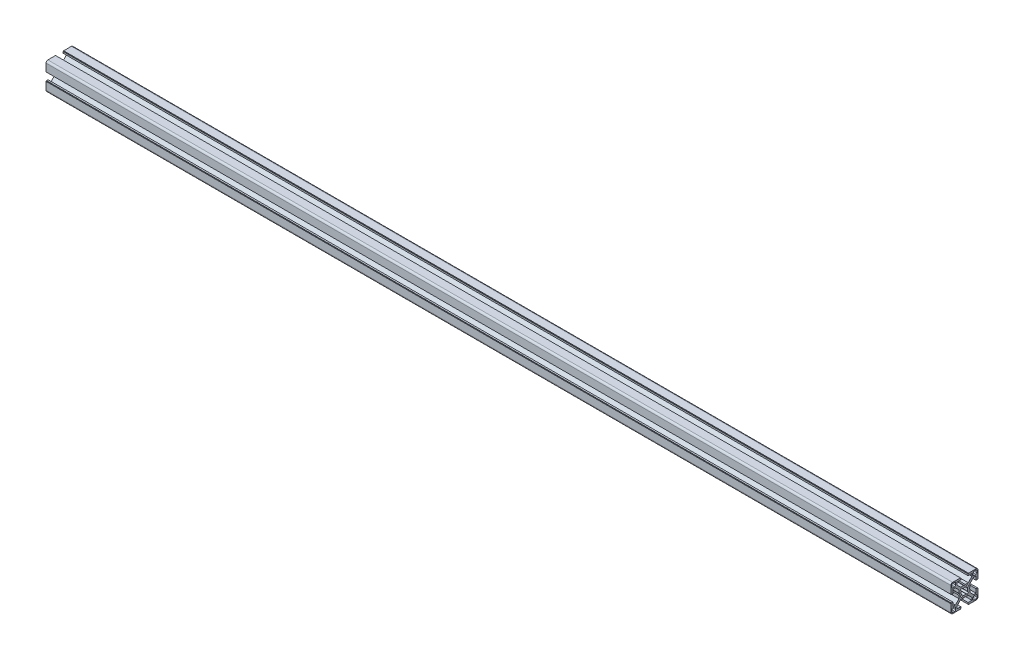
SolidWorks part; units mm, degrees
ref_plane "Piano frontale" through (0, 0, 0) normal (0, 0, 1) x (1, 0, 0)
ref_plane "Piano superiore" through (0, 0, 0) normal (0, 1, 0) x (1, 0, 0)
ref_plane "Piano destro" through (0, 0, 0) normal (1, 0, 0) x (0, 0, -1)
ref_plane "Piano1" through (0, 0, 0) normal (-1, 0, 0) x (0, -1, 0)
sketch "Schizzo1" plane through (0, 0, 0) normal (-1, 0, 0) x (0, -1, 0)
  line L0 (-3.1172, 4.5314) -> (-1.6168, 3.2724)
  line L1 (1.6168, 3.2724) -> (3.1172, 4.5314)
  line L2 (4.5314, 3.1172) -> (3.2724, 1.6168)
  line L3 (3.2724, -1.6168) -> (4.5314, -3.1172)
  line L4 (3.1172, -4.5314) -> (1.6168, -3.2724)
  line L5 (-1.6168, -3.2724) -> (-3.1172, -4.5314)
  line L6 (-4.5314, -3.1172) -> (-3.2724, -1.6168)
  line L7 (-3.2724, 1.6168) -> (-4.5314, 3.1172)
  line L8 (12.85, 9.7) -> (10.7, 9.7)
  line L9 (9.7, 10.7) -> (9.7, 12.85)
  line L10 (10.7, 13.85) -> (12.85, 13.85)
  line L11 (13.85, 12.85) -> (13.85, 10.7)
  line L12 (-9.7, 12.85) -> (-9.7, 10.7)
  line L13 (-10.7, 9.7) -> (-12.85, 9.7)
  line L14 (-13.85, 10.7) -> (-13.85, 12.85)
  line L15 (-12.85, 13.85) -> (-10.7, 13.85)
  line L16 (-12.85, -9.7) -> (-10.7, -9.7)
  line L17 (-9.7, -10.7) -> (-9.7, -12.85)
  line L18 (-10.7, -13.85) -> (-12.85, -13.85)
  line L19 (-13.85, -12.85) -> (-13.85, -10.7)
  line L20 (9.7, -12.85) -> (9.7, -10.7)
  line L21 (10.7, -9.7) -> (12.85, -9.7)
  line L22 (13.85, -10.7) -> (13.85, -12.85)
  line L23 (12.85, -13.85) -> (10.7, -13.85)
  line L24 (-10.0531, 8.25) -> (-6, 4.1969)
  line L25 (-6, 4.1969) -> (-6, 0.9196)
  line L26 (-6, 0.9196) -> (-5.4691, 0)
  line L27 (-5.4691, 0) -> (-6, -0.9196)
  line L28 (-6, -0.9196) -> (-6, -4.1969)
  line L29 (-6, -4.1969) -> (-10.0531, -8.25)
  line L30 (-10.0531, -8.25) -> (-12.8031, -8.25)
  line L31 (-12.8031, -8.25) -> (-12.8, -4)
  line L32 (-12.8, -4) -> (-14.5, -4)
  line L33 (-14.5, -4) -> (-14.5, -4.5)
  line L34 (-14.5, -4.5) -> (-15, -4.5)
  line L35 (-15, -4.5) -> (-15, -13)
  line L36 (-13, -15) -> (-4.5, -15)
  line L37 (-4.5, -15) -> (-4.5, -14.5)
  line L38 (-4.5, -14.5) -> (-4, -14.5)
  line L39 (-4, -14.5) -> (-4, -12.8)
  line L40 (-4, -12.8) -> (-8.25, -12.8031)
  line L41 (-8.25, -12.8031) -> (-8.25, -10.0531)
  line L42 (-8.25, -10.0531) -> (-4.1969, -6)
  line L43 (-4.1969, -6) -> (-0.9196, -6)
  line L44 (-0.9196, -6) -> (0, -5.4691)
  line L45 (0, -5.4691) -> (0.9196, -6)
  line L46 (0.9196, -6) -> (4.1969, -6)
  line L47 (4.1969, -6) -> (8.25, -10.0531)
  line L48 (8.25, -10.0531) -> (8.25, -12.8031)
  line L49 (8.25, -12.8031) -> (4, -12.8)
  line L50 (4, -12.8) -> (4, -14.5)
  line L51 (4, -14.5) -> (4.5, -14.5)
  line L52 (4.5, -14.5) -> (4.5, -15)
  line L53 (4.5, -15) -> (13, -15)
  line L54 (15, -13) -> (15, -4.5)
  line L55 (15, -4.5) -> (14.5, -4.5)
  line L56 (14.5, -4.5) -> (14.5, -4)
  line L57 (14.5, -4) -> (12.8, -4)
  line L58 (12.8, -4) -> (12.8031, -8.25)
  line L59 (12.8031, -8.25) -> (10.0531, -8.25)
  line L60 (10.0531, -8.25) -> (6, -4.1969)
  line L61 (6, -4.1969) -> (6, -0.9196)
  line L62 (6, -0.9196) -> (5.4691, 0)
  line L63 (5.4691, 0) -> (6, 0.9196)
  line L64 (6, 0.9196) -> (6, 4.1969)
  line L65 (6, 4.1969) -> (10.0531, 8.25)
  line L66 (10.0531, 8.25) -> (12.8031, 8.25)
  line L67 (12.8031, 8.25) -> (12.8, 4)
  line L68 (12.8, 4) -> (14.5, 4)
  line L69 (14.5, 4) -> (14.5, 4.5)
  line L70 (14.5, 4.5) -> (15, 4.5)
  line L71 (15, 4.5) -> (15, 13)
  line L72 (13, 15) -> (4.5, 15)
  line L73 (4.5, 15) -> (4.5, 14.5)
  line L74 (4.5, 14.5) -> (4, 14.5)
  line L75 (4, 14.5) -> (4, 12.8)
  line L76 (4, 12.8) -> (8.25, 12.8031)
  line L77 (8.25, 12.8031) -> (8.25, 10.0531)
  line L78 (8.25, 10.0531) -> (4.1969, 6)
  line L79 (4.1969, 6) -> (0.9196, 6)
  line L80 (0.9196, 6) -> (0, 5.4691)
  line L81 (0, 5.4691) -> (-0.9196, 6)
  line L82 (-0.9196, 6) -> (-4.1969, 6)
  line L83 (-4.1969, 6) -> (-8.25, 10.0531)
  line L84 (-8.25, 10.0531) -> (-8.25, 12.8031)
  line L85 (-8.25, 12.8031) -> (-4, 12.8)
  line L86 (-4, 12.8) -> (-4, 14.5)
  line L87 (-4, 14.5) -> (-4.5, 14.5)
  line L88 (-4.5, 14.5) -> (-4.5, 15)
  line L89 (-4.5, 15) -> (-13, 15)
  line L90 (-15, 13) -> (-15, 4.5)
  line L91 (-15, 4.5) -> (-14.5, 4.5)
  line L92 (-14.5, 4.5) -> (-14.5, 4)
  line L93 (-14.5, 4) -> (-12.8, 4)
  line L94 (-12.8, 4) -> (-12.8031, 8.25)
  line L95 (-12.8031, 8.25) -> (-10.0531, 8.25)
  arc A0 (-1.6168, 3.2724) -> (1.6168, 3.2724) centre (0, 0) cw
  arc A1 (3.1172, 4.5314) -> (4.5314, 3.1172) centre (0, 0) cw
  arc A2 (3.2724, 1.6168) -> (3.2724, -1.6168) centre (0, 0) cw
  arc A3 (4.5314, -3.1172) -> (3.1172, -4.5314) centre (0, 0) cw
  arc A4 (1.6168, -3.2724) -> (-1.6168, -3.2724) centre (0, 0) cw
  arc A5 (-3.1172, -4.5314) -> (-4.5314, -3.1172) centre (0, 0) cw
  arc A6 (-3.2724, -1.6168) -> (-3.2724, 1.6168) centre (0, 0) cw
  arc A7 (-4.5314, 3.1172) -> (-3.1172, 4.5314) centre (0, 0) cw
  arc A8 (10.7, 9.7) -> (9.7, 10.7) centre (10.7, 10.7) cw
  arc A9 (9.7, 12.85) -> (10.7, 13.85) centre (10.7, 12.85) cw
  arc A10 (12.85, 13.85) -> (13.85, 12.85) centre (12.85, 12.85) cw
  arc A11 (13.85, 10.7) -> (12.85, 9.7) centre (12.85, 10.7) cw
  arc A12 (-9.7, 10.7) -> (-10.7, 9.7) centre (-10.7, 10.7) cw
  arc A13 (-12.85, 9.7) -> (-13.85, 10.7) centre (-12.85, 10.7) cw
  arc A14 (-13.85, 12.85) -> (-12.85, 13.85) centre (-12.85, 12.85) cw
  arc A15 (-10.7, 13.85) -> (-9.7, 12.85) centre (-10.7, 12.85) cw
  arc A16 (-10.7, -9.7) -> (-9.7, -10.7) centre (-10.7, -10.7) cw
  arc A17 (-9.7, -12.85) -> (-10.7, -13.85) centre (-10.7, -12.85) cw
  arc A18 (-12.85, -13.85) -> (-13.85, -12.85) centre (-12.85, -12.85) cw
  arc A19 (-13.85, -10.7) -> (-12.85, -9.7) centre (-12.85, -10.7) cw
  arc A20 (9.7, -10.7) -> (10.7, -9.7) centre (10.7, -10.7) cw
  arc A21 (12.85, -9.7) -> (13.85, -10.7) centre (12.85, -10.7) cw
  arc A22 (13.85, -12.85) -> (12.85, -13.85) centre (12.85, -12.85) cw
  arc A23 (10.7, -13.85) -> (9.7, -12.85) centre (10.7, -12.85) cw
  arc A24 (-15, -13) -> (-13, -15) centre (-13, -13) ccw
  arc A25 (13, -15) -> (15, -13) centre (13, -13) ccw
  arc A26 (15, 13) -> (13, 15) centre (13, 13) ccw
  arc A27 (-13, 15) -> (-15, 13) centre (-13, 13) ccw
extrude "Estrusione-Estrusione1" add sketch "Schizzo1" against normal blind 1000
